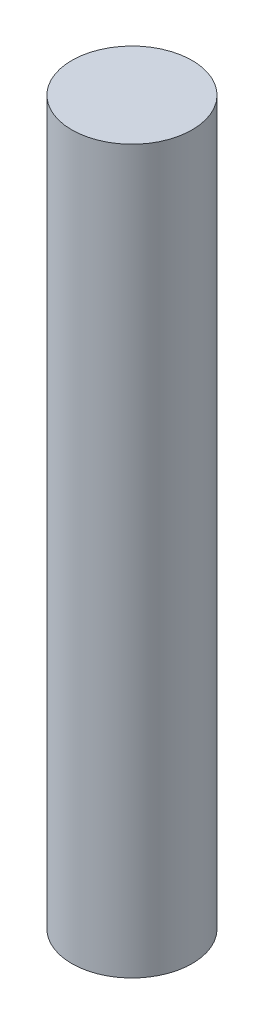
SolidWorks part; units mm, degrees
material "Plain Carbon Steel"
ref_plane "Front Plane" through (0, 0, 0) normal (0, 0, 1) x (1, 0, 0)
ref_plane "Top Plane" through (0, 0, 0) normal (0, 1, 0) x (1, 0, 0)
ref_plane "Right Plane" through (0, 0, 0) normal (1, 0, 0) x (0, 0, -1)
sketch "Sketch1" plane through (0, 0, 0) normal (0, 1, 0) x (1, 0, 0)
  circle A0 centre (0, 0) radius 4.7625
  dimension "D1" = 9.525
extrude "Boss-Extrude1" add sketch "Sketch1" along normal blind 57.15
